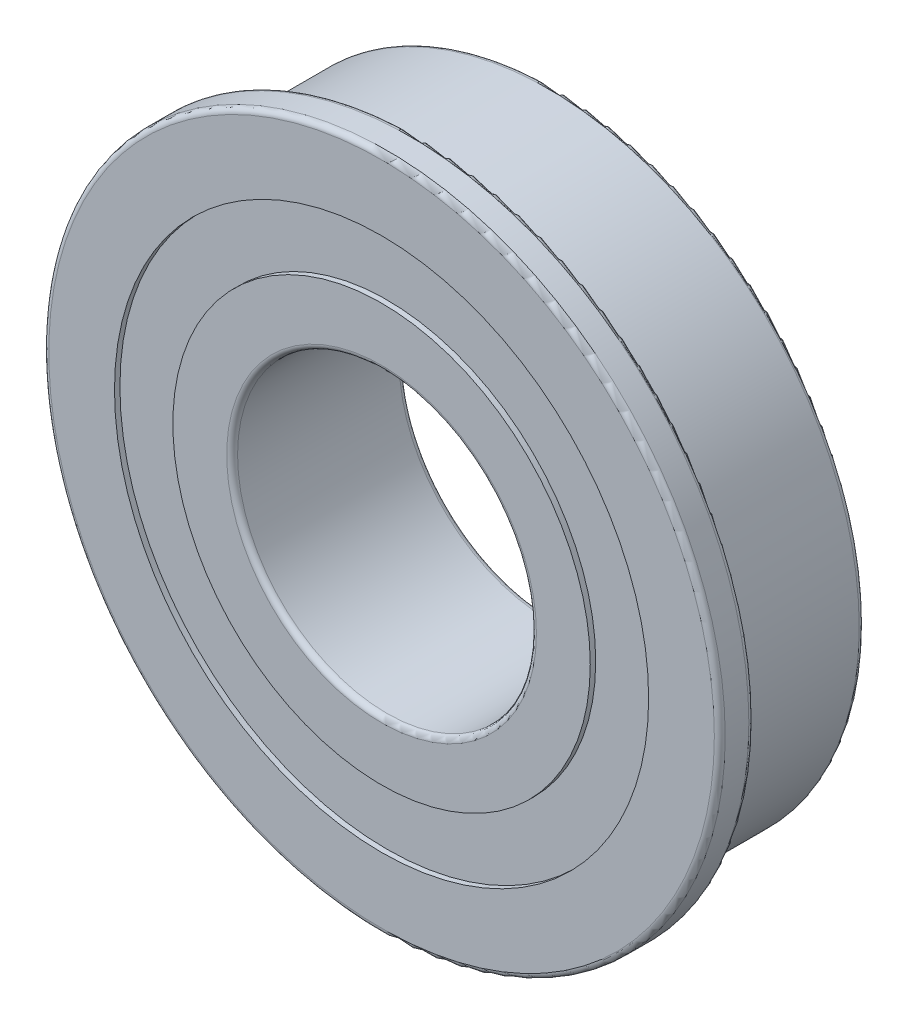
SolidWorks part; units mm, degrees
ref_plane "Front" through (0, 0, 0) normal (0, 0, 1) x (1, 0, 0)
ref_plane "Top" through (0, 0, 0) normal (0, 1, 0) x (1, 0, 0)
ref_plane "Right" through (0, 0, 0) normal (1, 0, 0) x (0, 0, -1)
sketch "Sketch1" plane through (0, 0, 0) normal (0, 1, 0) x (1, 0, 0)
  line L0 (14.0375, 3.9688) -> (12.2875, 3.9688)
  line L1 (12.2875, 3.9688) -> (12.2875, 3.7188)
  line L2 (12.2875, 3.7188) -> (9.602, 3.7188)
  line L3 (9.602, 3.7188) -> (9.602, 3.9688)
  line L4 (9.602, 3.9688) -> (7.125, 3.9688)
  line L5 (6.875, 3.7188) -> (6.875, -3.7188)
  line L6 (7.125, -3.9688) -> (9.602, -3.9688)
  line L7 (9.602, -3.9688) -> (9.602, -3.7188)
  line L8 (9.602, -3.7188) -> (12.2875, -3.7188)
  line L9 (12.2875, -3.7188) -> (12.2875, -3.9688)
  line L10 (12.2875, -3.9688) -> (15.31, -3.9688)
  line L11 (15.56, -3.7188) -> (15.56, -2.6313)
  line L12 (15.31, -2.3812) -> (14.2875, -2.3812)
  line L13 (14.071, -2.0062) -> (14.2875, -1.6312)
  line L14 (14.2875, -1.6312) -> (14.2875, 3.7188)
  line L15 (0, 3.97) -> (0, -3.97) construction
  arc A0 (7.125, 3.9688) -> (6.875, 3.7188) centre (7.125, 3.7188) ccw
  arc A1 (6.875, -3.7188) -> (7.125, -3.9688) centre (7.125, -3.7188) ccw
  arc A2 (15.31, -3.9688) -> (15.56, -3.7188) centre (15.31, -3.7188) ccw
  arc A3 (15.56, -2.6313) -> (15.31, -2.3812) centre (15.31, -2.6313) ccw
  arc A4 (14.2875, -2.3812) -> (14.071, -2.0062) centre (14.2875, -2.1312) cw
  arc A5 (14.2875, 3.7188) -> (14.0375, 3.9688) centre (14.0375, 3.7188) ccw
revolve "Revolve1" add sketch "Sketch1" angle 360 about L15
